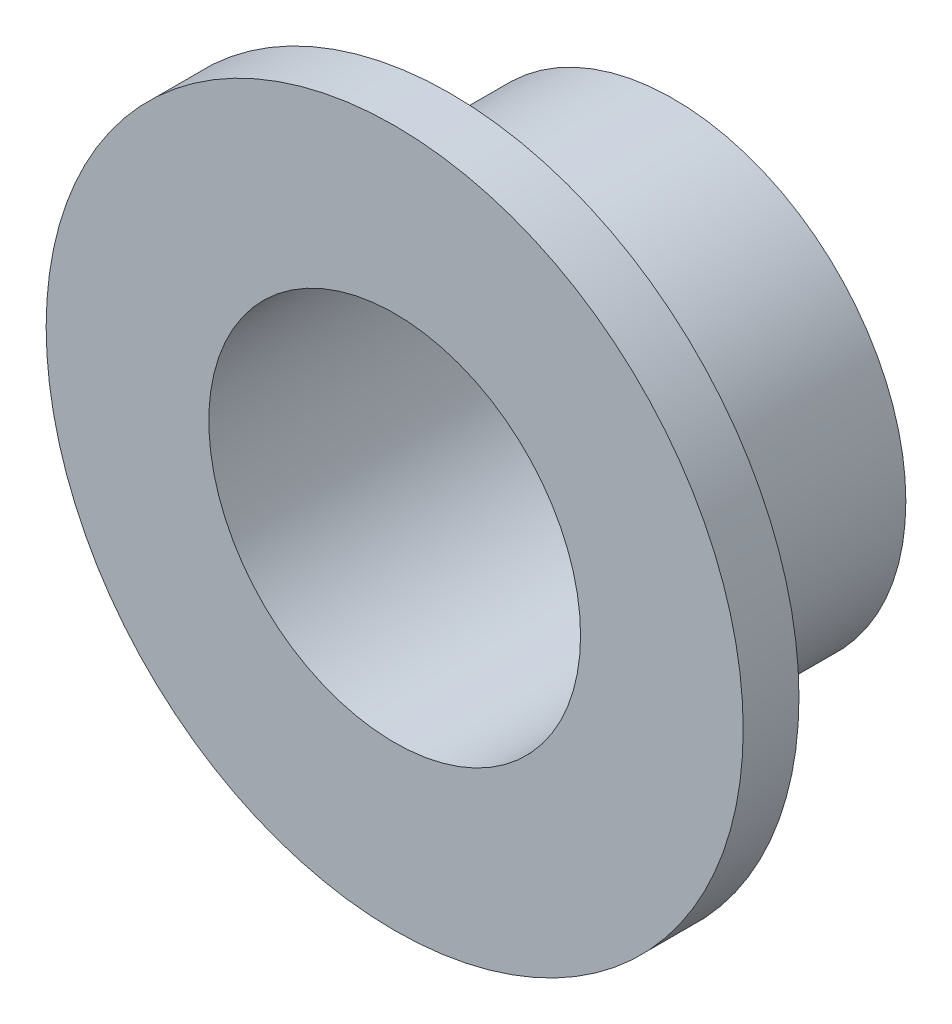
SolidWorks part; units mm, degrees
material "Tin Bearing Bronze"
ref_plane "Front Plane" through (0, 0, 0) normal (0, 0, 1) x (1, 0, 0)
ref_plane "Top Plane" through (0, 0, 0) normal (0, 1, 0) x (1, 0, 0)
ref_plane "Right Plane" through (0, 0, 0) normal (1, 0, 0) x (0, 0, -1)
sketch "Sketch1" plane through (0, 0, 0) normal (1, 0, 0) x (0, 0, -1)
  line L0 (0, 4) -> (0, 7.5)
  line L1 (0, 7.5) -> (1.2, 7.5)
  line L2 (1.2, 7.5) -> (1.2, 5)
  line L3 (1.2, 5) -> (6, 5)
  line L4 (6, 5) -> (6, 4)
  line L5 (6, 4) -> (0, 4)
  line L6 (0, 0) -> (17.5023, 0) construction
  dimension "D1" = 4
  dimension "D2" = 5
  dimension "D3" = 7.5
  dimension "D4" = 1.2
  dimension "D5" = 6
revolve "Revolve1" add sketch "Sketch1" angle 360 about L6
